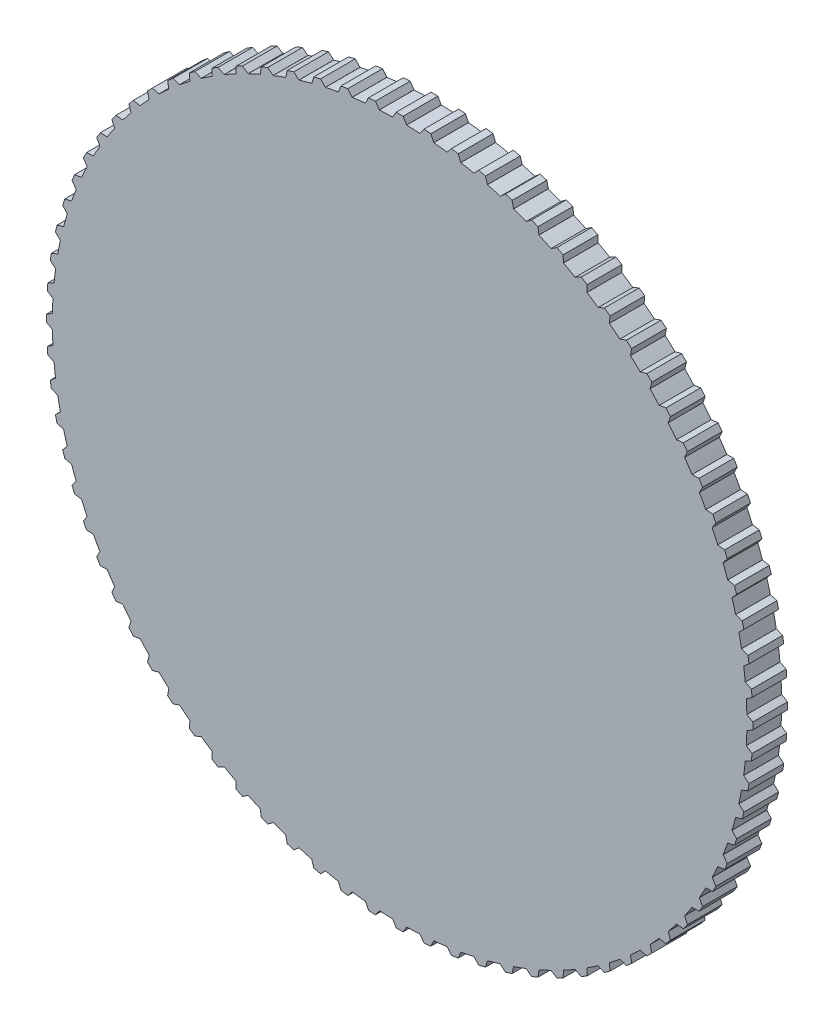
SolidWorks part; units mm, degrees
ref_plane "Front Plane" through (0, 0, 0) normal (0, 0, 1) x (1, 0, 0)
ref_plane "Top Plane" through (0, 0, 0) normal (0, 1, 0) x (1, 0, 0)
ref_plane "Right Plane" through (0, 0, 0) normal (1, 0, 0) x (0, 0, -1)
sketch "Sketch1" plane through (0, 0, 0) normal (0, 0, 1) x (1, 0, 0)
  line L1 (0, 101.7) -> (1, 101.7)
  line L2 (0, 101.7) -> (-1, 101.7)
  line L5 (-1, 101.7) -> (-2, 100)
  line L6 (1, 101.7) -> (2, 100)
  line L7 (-2, 100) -> (-1.9996, 99.98)
  line L8 (2, 100) -> (1.9996, 99.98)
  line L9 (6.9824, 101.465) -> (5.8521, 99.8487)
  line L10 (7.9793, 101.3865) -> (6.9824, 101.465)
  line L11 (7.9793, 101.3865) -> (8.9762, 101.308)
  line L12 (8.9762, 101.308) -> (9.8397, 99.5348)
  line L13 (5.8521, 99.8487) -> (5.8509, 99.8287)
  line L14 (9.8397, 99.5348) -> (9.8378, 99.5149)
  line L15 (14.9217, 100.6043) -> (13.6681, 99.0817)
  line L16 (15.9094, 100.4479) -> (14.9217, 100.6043)
  line L17 (15.9094, 100.4479) -> (16.8971, 100.2915)
  line L18 (16.8971, 100.2915) -> (17.6188, 98.456)
  line L19 (13.6681, 99.0817) -> (13.6653, 99.0619)
  line L20 (17.6188, 98.456) -> (17.6153, 98.4363)
  line L21 (22.769, 99.1235) -> (21.3998, 97.7039)
  line L22 (23.7414, 98.89) -> (22.769, 99.1235)
  line L23 (23.7414, 98.89) -> (24.7138, 98.6566)
  line L24 (24.7138, 98.6566) -> (25.2893, 96.7701)
  line L25 (21.3998, 97.7039) -> (21.3955, 97.6843)
  line L26 (25.2893, 96.7701) -> (25.2842, 96.7508)
  line L27 (30.476, 97.0315) -> (28.9996, 95.7237)
  line L28 (31.427, 96.7224) -> (30.476, 97.0315)
  line L29 (31.427, 96.7224) -> (32.3781, 96.4134)
  line L30 (32.3781, 96.4134) -> (32.8038, 94.4876)
  line L31 (28.9996, 95.7237) -> (28.9938, 95.7045)
  line L32 (32.8038, 94.4876) -> (32.7973, 94.4687)
  line L33 (37.995, 94.3412) -> (36.4206, 93.1533)
  line L34 (38.9189, 93.9585) -> (37.995, 94.3412)
  line L35 (38.9189, 93.9585) -> (39.8428, 93.5759)
  line L36 (39.8428, 93.5759) -> (40.1161, 91.6226)
  line L37 (36.4206, 93.1533) -> (36.4133, 93.1347)
  line L38 (40.1161, 91.6226) -> (40.1081, 91.6043)
  line L39 (45.2798, 91.0694) -> (43.617, 90.0086)
  line L40 (46.1708, 90.6154) -> (45.2798, 91.0694)
  line L41 (46.1708, 90.6154) -> (47.0618, 90.1614)
  line L42 (47.0618, 90.1614) -> (47.1811, 88.1927)
  line L43 (43.617, 90.0086) -> (43.6083, 89.9906)
  line L44 (47.1811, 88.1927) -> (47.1716, 88.175)
  line L45 (52.2855, 87.236) -> (50.5446, 86.309)
  line L46 (53.1381, 86.7135) -> (52.2855, 87.236)
  line L47 (53.1381, 86.7135) -> (53.9907, 86.191)
  line L48 (53.9907, 86.191) -> (53.9551, 84.219)
  line L49 (50.5446, 86.309) -> (50.5345, 86.2918)
  line L50 (53.9551, 84.219) -> (53.9443, 84.2022)
  line L51 (58.9687, 82.8648) -> (57.1605, 82.0773)
  line L52 (59.7778, 82.277) -> (58.9687, 82.8648)
  line L53 (59.7778, 82.277) -> (60.5868, 81.6892)
  line L54 (60.5868, 81.6892) -> (60.3966, 79.7261)
  line L55 (57.1605, 82.0773) -> (57.1491, 82.0609)
  line L56 (60.3966, 79.7261) -> (60.3845, 79.7102)
  line L57 (65.2885, 77.9827) -> (63.424, 77.3395)
  line L58 (66.0489, 77.3333) -> (65.2885, 77.9827)
  line L59 (66.0489, 77.3333) -> (66.8093, 76.6838)
  line L60 (66.8093, 76.6838) -> (66.4656, 74.7417)
  line L61 (63.424, 77.3395) -> (63.4113, 77.324)
  line L62 (66.4656, 74.7417) -> (66.4523, 74.7268)
  line L63 (71.2057, 72.6199) -> (69.2965, 72.1249)
  line L64 (71.9128, 71.9128) -> (71.2057, 72.6199)
  line L65 (71.9128, 71.9128) -> (72.6199, 71.2057)
  line L66 (72.6199, 71.2057) -> (72.1249, 69.2965)
  line L67 (69.2965, 72.1249) -> (69.2826, 72.1105)
  line L68 (72.1249, 69.2965) -> (72.1105, 69.2826)
  line L69 (76.6838, 66.8093) -> (74.7417, 66.4656)
  line L70 (77.3333, 66.0489) -> (76.6838, 66.8093)
  line L71 (77.3333, 66.0489) -> (77.9827, 65.2885)
  line L72 (77.9827, 65.2885) -> (77.3395, 63.424)
  line L73 (74.7417, 66.4656) -> (74.7268, 66.4523)
  line L74 (77.3395, 63.424) -> (77.324, 63.4113)
  line L75 (81.6892, 60.5868) -> (79.7261, 60.3966)
  line L76 (82.277, 59.7778) -> (81.6892, 60.5868)
  line L77 (82.277, 59.7778) -> (82.8648, 58.9687)
  line L78 (82.8648, 58.9687) -> (82.0773, 57.1605)
  line L79 (79.7261, 60.3966) -> (79.7102, 60.3845)
  line L80 (82.0773, 57.1605) -> (82.0609, 57.1491)
  line L81 (86.191, 53.9907) -> (84.219, 53.9551)
  line L82 (86.7135, 53.1381) -> (86.191, 53.9907)
  line L83 (86.7135, 53.1381) -> (87.236, 52.2855)
  line L84 (87.236, 52.2855) -> (86.309, 50.5446)
  line L85 (84.219, 53.9551) -> (84.2022, 53.9443)
  line L86 (86.309, 50.5446) -> (86.2918, 50.5345)
  line L87 (90.1614, 47.0618) -> (88.1927, 47.1811)
  line L88 (90.6154, 46.1708) -> (90.1614, 47.0618)
  line L89 (90.6154, 46.1708) -> (91.0694, 45.2798)
  line L90 (91.0694, 45.2798) -> (90.0086, 43.617)
  line L91 (88.1927, 47.1811) -> (88.175, 47.1716)
  line L92 (90.0086, 43.617) -> (89.9906, 43.6083)
  line L93 (93.5759, 39.8428) -> (91.6226, 40.1161)
  line L94 (93.9585, 38.9189) -> (93.5759, 39.8428)
  line L95 (93.9585, 38.9189) -> (94.3412, 37.995)
  line L96 (94.3412, 37.995) -> (93.1533, 36.4206)
  line L97 (91.6226, 40.1161) -> (91.6043, 40.1081)
  line L98 (93.1533, 36.4206) -> (93.1347, 36.4133)
  line L99 (96.4134, 32.3781) -> (94.4876, 32.8038)
  line L100 (96.7224, 31.427) -> (96.4134, 32.3781)
  line L101 (96.7224, 31.427) -> (97.0315, 30.476)
  line L102 (97.0315, 30.476) -> (95.7237, 28.9996)
  line L103 (94.4876, 32.8038) -> (94.4687, 32.7973)
  line L104 (95.7237, 28.9996) -> (95.7045, 28.9938)
  line L105 (98.6566, 24.7138) -> (96.7701, 25.2893)
  line L106 (98.89, 23.7414) -> (98.6566, 24.7138)
  line L107 (98.89, 23.7414) -> (99.1235, 22.769)
  line L108 (99.1235, 22.769) -> (97.7039, 21.3998)
  line L109 (96.7701, 25.2893) -> (96.7508, 25.2842)
  line L110 (97.7039, 21.3998) -> (97.6843, 21.3955)
  line L111 (100.2915, 16.8971) -> (98.456, 17.6188)
  line L112 (100.4479, 15.9094) -> (100.2915, 16.8971)
  line L113 (100.4479, 15.9094) -> (100.6043, 14.9217)
  line L114 (100.6043, 14.9217) -> (99.0817, 13.6681)
  line L115 (98.456, 17.6188) -> (98.4363, 17.6153)
  line L116 (99.0817, 13.6681) -> (99.0619, 13.6653)
  line L117 (101.308, 8.9762) -> (99.5348, 9.8397)
  line L118 (101.3865, 7.9793) -> (101.308, 8.9762)
  line L119 (101.3865, 7.9793) -> (101.465, 6.9824)
  line L120 (101.465, 6.9824) -> (99.8487, 5.8521)
  line L121 (99.5348, 9.8397) -> (99.5149, 9.8378)
  line L122 (99.8487, 5.8521) -> (99.8287, 5.8509)
  line L123 (101.7, 1) -> (100, 2)
  line L124 (101.7, 0) -> (101.7, 1)
  line L125 (101.7, 0) -> (101.7, -1)
  line L126 (101.7, -1) -> (100, -2)
  line L127 (100, 2) -> (99.98, 1.9996)
  line L128 (100, -2) -> (99.98, -1.9996)
  line L129 (101.465, -6.9824) -> (99.8487, -5.8521)
  line L130 (101.3865, -7.9793) -> (101.465, -6.9824)
  line L131 (101.3865, -7.9793) -> (101.308, -8.9762)
  line L132 (101.308, -8.9762) -> (99.5348, -9.8397)
  line L133 (99.8487, -5.8521) -> (99.8287, -5.8509)
  line L134 (99.5348, -9.8397) -> (99.5149, -9.8378)
  line L135 (100.6043, -14.9217) -> (99.0817, -13.6681)
  line L136 (100.4479, -15.9094) -> (100.6043, -14.9217)
  line L137 (100.4479, -15.9094) -> (100.2915, -16.8971)
  line L138 (100.2915, -16.8971) -> (98.456, -17.6188)
  line L139 (99.0817, -13.6681) -> (99.0619, -13.6653)
  line L140 (98.456, -17.6188) -> (98.4363, -17.6153)
  line L141 (99.1235, -22.769) -> (97.7039, -21.3998)
  line L142 (98.89, -23.7414) -> (99.1235, -22.769)
  line L143 (98.89, -23.7414) -> (98.6566, -24.7138)
  line L144 (98.6566, -24.7138) -> (96.7701, -25.2893)
  line L145 (97.7039, -21.3998) -> (97.6843, -21.3955)
  line L146 (96.7701, -25.2893) -> (96.7508, -25.2842)
  line L147 (97.0315, -30.476) -> (95.7237, -28.9996)
  line L148 (96.7224, -31.427) -> (97.0315, -30.476)
  line L149 (96.7224, -31.427) -> (96.4134, -32.3781)
  line L150 (96.4134, -32.3781) -> (94.4876, -32.8038)
  line L151 (95.7237, -28.9996) -> (95.7045, -28.9938)
  line L152 (94.4876, -32.8038) -> (94.4687, -32.7973)
  line L153 (94.3412, -37.995) -> (93.1533, -36.4206)
  line L154 (93.9585, -38.9189) -> (94.3412, -37.995)
  line L155 (93.9585, -38.9189) -> (93.5759, -39.8428)
  line L156 (93.5759, -39.8428) -> (91.6226, -40.1161)
  line L157 (93.1533, -36.4206) -> (93.1347, -36.4133)
  line L158 (91.6226, -40.1161) -> (91.6043, -40.1081)
  line L159 (91.0694, -45.2798) -> (90.0086, -43.617)
  line L160 (90.6154, -46.1708) -> (91.0694, -45.2798)
  line L161 (90.6154, -46.1708) -> (90.1614, -47.0618)
  line L162 (90.1614, -47.0618) -> (88.1927, -47.1811)
  line L163 (90.0086, -43.617) -> (89.9906, -43.6083)
  line L164 (88.1927, -47.1811) -> (88.175, -47.1716)
  line L165 (87.236, -52.2855) -> (86.309, -50.5446)
  line L166 (86.7135, -53.1381) -> (87.236, -52.2855)
  line L167 (86.7135, -53.1381) -> (86.191, -53.9907)
  line L168 (86.191, -53.9907) -> (84.219, -53.9551)
  line L169 (86.309, -50.5446) -> (86.2918, -50.5345)
  line L170 (84.219, -53.9551) -> (84.2022, -53.9443)
  line L171 (82.8648, -58.9687) -> (82.0773, -57.1605)
  line L172 (82.277, -59.7778) -> (82.8648, -58.9687)
  line L173 (82.277, -59.7778) -> (81.6892, -60.5868)
  line L174 (81.6892, -60.5868) -> (79.7261, -60.3966)
  line L175 (82.0773, -57.1605) -> (82.0609, -57.1491)
  line L176 (79.7261, -60.3966) -> (79.7102, -60.3845)
  line L177 (77.9827, -65.2885) -> (77.3395, -63.424)
  line L178 (77.3333, -66.0489) -> (77.9827, -65.2885)
  line L179 (77.3333, -66.0489) -> (76.6838, -66.8093)
  line L180 (76.6838, -66.8093) -> (74.7417, -66.4656)
  line L181 (77.3395, -63.424) -> (77.324, -63.4113)
  line L182 (74.7417, -66.4656) -> (74.7268, -66.4523)
  line L183 (72.6199, -71.2057) -> (72.1249, -69.2965)
  line L184 (71.9128, -71.9128) -> (72.6199, -71.2057)
  line L185 (71.9128, -71.9128) -> (71.2057, -72.6199)
  line L186 (71.2057, -72.6199) -> (69.2965, -72.1249)
  line L187 (72.1249, -69.2965) -> (72.1105, -69.2826)
  line L188 (69.2965, -72.1249) -> (69.2826, -72.1105)
  line L189 (66.8093, -76.6838) -> (66.4656, -74.7417)
  line L190 (66.0489, -77.3333) -> (66.8093, -76.6838)
  line L191 (66.0489, -77.3333) -> (65.2885, -77.9827)
  line L192 (65.2885, -77.9827) -> (63.424, -77.3395)
  line L193 (66.4656, -74.7417) -> (66.4523, -74.7268)
  line L194 (63.424, -77.3395) -> (63.4113, -77.324)
  line L195 (60.5868, -81.6892) -> (60.3966, -79.7261)
  line L196 (59.7778, -82.277) -> (60.5868, -81.6892)
  line L197 (59.7778, -82.277) -> (58.9687, -82.8648)
  line L198 (58.9687, -82.8648) -> (57.1605, -82.0773)
  line L199 (60.3966, -79.7261) -> (60.3845, -79.7102)
  line L200 (57.1605, -82.0773) -> (57.1491, -82.0609)
  line L201 (53.9907, -86.191) -> (53.9551, -84.219)
  line L202 (53.1381, -86.7135) -> (53.9907, -86.191)
  line L203 (53.1381, -86.7135) -> (52.2855, -87.236)
  line L204 (52.2855, -87.236) -> (50.5446, -86.309)
  line L205 (53.9551, -84.219) -> (53.9443, -84.2022)
  line L206 (50.5446, -86.309) -> (50.5345, -86.2918)
  line L207 (47.0618, -90.1614) -> (47.1811, -88.1927)
  line L208 (46.1708, -90.6154) -> (47.0618, -90.1614)
  line L209 (46.1708, -90.6154) -> (45.2798, -91.0694)
  line L210 (45.2798, -91.0694) -> (43.617, -90.0086)
  line L211 (47.1811, -88.1927) -> (47.1716, -88.175)
  line L212 (43.617, -90.0086) -> (43.6083, -89.9906)
  line L213 (39.8428, -93.5759) -> (40.1161, -91.6226)
  line L214 (38.9189, -93.9585) -> (39.8428, -93.5759)
  line L215 (38.9189, -93.9585) -> (37.995, -94.3412)
  line L216 (37.995, -94.3412) -> (36.4206, -93.1533)
  line L217 (40.1161, -91.6226) -> (40.1081, -91.6043)
  line L218 (36.4206, -93.1533) -> (36.4133, -93.1347)
  line L219 (32.3781, -96.4134) -> (32.8038, -94.4876)
  line L220 (31.427, -96.7224) -> (32.3781, -96.4134)
  line L221 (31.427, -96.7224) -> (30.476, -97.0315)
  line L222 (30.476, -97.0315) -> (28.9996, -95.7237)
  line L223 (32.8038, -94.4876) -> (32.7973, -94.4687)
  line L224 (28.9996, -95.7237) -> (28.9938, -95.7045)
  line L225 (24.7138, -98.6566) -> (25.2893, -96.7701)
  line L226 (23.7414, -98.89) -> (24.7138, -98.6566)
  line L227 (23.7414, -98.89) -> (22.769, -99.1235)
  line L228 (22.769, -99.1235) -> (21.3998, -97.7039)
  line L229 (25.2893, -96.7701) -> (25.2842, -96.7508)
  line L230 (21.3998, -97.7039) -> (21.3955, -97.6843)
  line L231 (16.8971, -100.2915) -> (17.6188, -98.456)
  line L232 (15.9094, -100.4479) -> (16.8971, -100.2915)
  line L233 (15.9094, -100.4479) -> (14.9217, -100.6043)
  line L234 (14.9217, -100.6043) -> (13.6681, -99.0817)
  line L235 (17.6188, -98.456) -> (17.6153, -98.4363)
  line L236 (13.6681, -99.0817) -> (13.6653, -99.0619)
  line L237 (8.9762, -101.308) -> (9.8397, -99.5348)
  line L238 (7.9793, -101.3865) -> (8.9762, -101.308)
  line L239 (7.9793, -101.3865) -> (6.9824, -101.465)
  line L240 (6.9824, -101.465) -> (5.8521, -99.8487)
  line L241 (9.8397, -99.5348) -> (9.8378, -99.5149)
  line L242 (5.8521, -99.8487) -> (5.8509, -99.8287)
  line L243 (1, -101.7) -> (2, -100)
  line L244 (0, -101.7) -> (1, -101.7)
  line L245 (0, -101.7) -> (-1, -101.7)
  line L246 (-1, -101.7) -> (-2, -100)
  line L247 (2, -100) -> (1.9996, -99.98)
  line L248 (-2, -100) -> (-1.9996, -99.98)
  line L249 (-6.9824, -101.465) -> (-5.8521, -99.8487)
  line L250 (-7.9793, -101.3865) -> (-6.9824, -101.465)
  line L251 (-7.9793, -101.3865) -> (-8.9762, -101.308)
  line L252 (-8.9762, -101.308) -> (-9.8397, -99.5348)
  line L253 (-5.8521, -99.8487) -> (-5.8509, -99.8287)
  line L254 (-9.8397, -99.5348) -> (-9.8378, -99.5149)
  line L255 (-14.9217, -100.6043) -> (-13.6681, -99.0817)
  line L256 (-15.9094, -100.4479) -> (-14.9217, -100.6043)
  line L257 (-15.9094, -100.4479) -> (-16.8971, -100.2915)
  line L258 (-16.8971, -100.2915) -> (-17.6188, -98.456)
  line L259 (-13.6681, -99.0817) -> (-13.6653, -99.0619)
  line L260 (-17.6188, -98.456) -> (-17.6153, -98.4363)
  line L261 (-22.769, -99.1235) -> (-21.3998, -97.7039)
  line L262 (-23.7414, -98.89) -> (-22.769, -99.1235)
  line L263 (-23.7414, -98.89) -> (-24.7138, -98.6566)
  line L264 (-24.7138, -98.6566) -> (-25.2893, -96.7701)
  line L265 (-21.3998, -97.7039) -> (-21.3955, -97.6843)
  line L266 (-25.2893, -96.7701) -> (-25.2842, -96.7508)
  line L267 (-30.476, -97.0315) -> (-28.9996, -95.7237)
  line L268 (-31.427, -96.7224) -> (-30.476, -97.0315)
  line L269 (-31.427, -96.7224) -> (-32.3781, -96.4134)
  line L270 (-32.3781, -96.4134) -> (-32.8038, -94.4876)
  line L271 (-28.9996, -95.7237) -> (-28.9938, -95.7045)
  line L272 (-32.8038, -94.4876) -> (-32.7973, -94.4687)
  line L273 (-37.995, -94.3412) -> (-36.4206, -93.1533)
  line L274 (-38.9189, -93.9585) -> (-37.995, -94.3412)
  line L275 (-38.9189, -93.9585) -> (-39.8428, -93.5759)
  line L276 (-39.8428, -93.5759) -> (-40.1161, -91.6226)
  line L277 (-36.4206, -93.1533) -> (-36.4133, -93.1347)
  line L278 (-40.1161, -91.6226) -> (-40.1081, -91.6043)
  line L279 (-45.2798, -91.0694) -> (-43.617, -90.0086)
  line L280 (-46.1708, -90.6154) -> (-45.2798, -91.0694)
  line L281 (-46.1708, -90.6154) -> (-47.0618, -90.1614)
  line L282 (-47.0618, -90.1614) -> (-47.1811, -88.1927)
  line L283 (-43.617, -90.0086) -> (-43.6083, -89.9906)
  line L284 (-47.1811, -88.1927) -> (-47.1716, -88.175)
  line L285 (-52.2855, -87.236) -> (-50.5446, -86.309)
  line L286 (-53.1381, -86.7135) -> (-52.2855, -87.236)
  line L287 (-53.1381, -86.7135) -> (-53.9907, -86.191)
  line L288 (-53.9907, -86.191) -> (-53.9551, -84.219)
  line L289 (-50.5446, -86.309) -> (-50.5345, -86.2918)
  line L290 (-53.9551, -84.219) -> (-53.9443, -84.2022)
  line L291 (-58.9687, -82.8648) -> (-57.1605, -82.0773)
  line L292 (-59.7778, -82.277) -> (-58.9687, -82.8648)
  line L293 (-59.7778, -82.277) -> (-60.5868, -81.6892)
  line L294 (-60.5868, -81.6892) -> (-60.3966, -79.7261)
  line L295 (-57.1605, -82.0773) -> (-57.1491, -82.0609)
  line L296 (-60.3966, -79.7261) -> (-60.3845, -79.7102)
  line L297 (-65.2885, -77.9827) -> (-63.424, -77.3395)
  line L298 (-66.0489, -77.3333) -> (-65.2885, -77.9827)
  line L299 (-66.0489, -77.3333) -> (-66.8093, -76.6838)
  line L300 (-66.8093, -76.6838) -> (-66.4656, -74.7417)
  line L301 (-63.424, -77.3395) -> (-63.4113, -77.324)
  line L302 (-66.4656, -74.7417) -> (-66.4523, -74.7268)
  line L303 (-71.2057, -72.6199) -> (-69.2965, -72.1249)
  line L304 (-71.9128, -71.9128) -> (-71.2057, -72.6199)
  line L305 (-71.9128, -71.9128) -> (-72.6199, -71.2057)
  line L306 (-72.6199, -71.2057) -> (-72.1249, -69.2965)
  line L307 (-69.2965, -72.1249) -> (-69.2826, -72.1105)
  line L308 (-72.1249, -69.2965) -> (-72.1105, -69.2826)
  line L309 (-76.6838, -66.8093) -> (-74.7417, -66.4656)
  line L310 (-77.3333, -66.0489) -> (-76.6838, -66.8093)
  line L311 (-77.3333, -66.0489) -> (-77.9827, -65.2885)
  line L312 (-77.9827, -65.2885) -> (-77.3395, -63.424)
  line L313 (-74.7417, -66.4656) -> (-74.7268, -66.4523)
  line L314 (-77.3395, -63.424) -> (-77.324, -63.4113)
  line L315 (-81.6892, -60.5868) -> (-79.7261, -60.3966)
  line L316 (-82.277, -59.7778) -> (-81.6892, -60.5868)
  line L317 (-82.277, -59.7778) -> (-82.8648, -58.9687)
  line L318 (-82.8648, -58.9687) -> (-82.0773, -57.1605)
  line L319 (-79.7261, -60.3966) -> (-79.7102, -60.3845)
  line L320 (-82.0773, -57.1605) -> (-82.0609, -57.1491)
  line L321 (-86.191, -53.9907) -> (-84.219, -53.9551)
  line L322 (-86.7135, -53.1381) -> (-86.191, -53.9907)
  line L323 (-86.7135, -53.1381) -> (-87.236, -52.2855)
  line L324 (-87.236, -52.2855) -> (-86.309, -50.5446)
  line L325 (-84.219, -53.9551) -> (-84.2022, -53.9443)
  line L326 (-86.309, -50.5446) -> (-86.2918, -50.5345)
  line L327 (-90.1614, -47.0618) -> (-88.1927, -47.1811)
  line L328 (-90.6154, -46.1708) -> (-90.1614, -47.0618)
  line L329 (-90.6154, -46.1708) -> (-91.0694, -45.2798)
  line L330 (-91.0694, -45.2798) -> (-90.0086, -43.617)
  line L331 (-88.1927, -47.1811) -> (-88.175, -47.1716)
  line L332 (-90.0086, -43.617) -> (-89.9906, -43.6083)
  line L333 (-93.5759, -39.8428) -> (-91.6226, -40.1161)
  line L334 (-93.9585, -38.9189) -> (-93.5759, -39.8428)
  line L335 (-93.9585, -38.9189) -> (-94.3412, -37.995)
  line L336 (-94.3412, -37.995) -> (-93.1533, -36.4206)
  line L337 (-91.6226, -40.1161) -> (-91.6043, -40.1081)
  line L338 (-93.1533, -36.4206) -> (-93.1347, -36.4133)
  line L339 (-96.4134, -32.3781) -> (-94.4876, -32.8038)
  line L340 (-96.7224, -31.427) -> (-96.4134, -32.3781)
  line L341 (-96.7224, -31.427) -> (-97.0315, -30.476)
  line L342 (-97.0315, -30.476) -> (-95.7237, -28.9996)
  line L343 (-94.4876, -32.8038) -> (-94.4687, -32.7973)
  line L344 (-95.7237, -28.9996) -> (-95.7045, -28.9938)
  line L345 (-98.6566, -24.7138) -> (-96.7701, -25.2893)
  line L346 (-98.89, -23.7414) -> (-98.6566, -24.7138)
  line L347 (-98.89, -23.7414) -> (-99.1235, -22.769)
  line L348 (-99.1235, -22.769) -> (-97.7039, -21.3998)
  line L349 (-96.7701, -25.2893) -> (-96.7508, -25.2842)
  line L350 (-97.7039, -21.3998) -> (-97.6843, -21.3955)
  line L351 (-100.2915, -16.8971) -> (-98.456, -17.6188)
  line L352 (-100.4479, -15.9094) -> (-100.2915, -16.8971)
  line L353 (-100.4479, -15.9094) -> (-100.6043, -14.9217)
  line L354 (-100.6043, -14.9217) -> (-99.0817, -13.6681)
  line L355 (-98.456, -17.6188) -> (-98.4363, -17.6153)
  line L356 (-99.0817, -13.6681) -> (-99.0619, -13.6653)
  line L357 (-101.308, -8.9762) -> (-99.5348, -9.8397)
  line L358 (-101.3865, -7.9793) -> (-101.308, -8.9762)
  line L359 (-101.3865, -7.9793) -> (-101.465, -6.9824)
  line L360 (-101.465, -6.9824) -> (-99.8487, -5.8521)
  line L361 (-99.5348, -9.8397) -> (-99.5149, -9.8378)
  line L362 (-99.8487, -5.8521) -> (-99.8287, -5.8509)
  line L363 (-101.7, -1) -> (-100, -2)
  line L364 (-101.7, 0) -> (-101.7, -1)
  line L365 (-101.7, 0) -> (-101.7, 1)
  line L366 (-101.7, 1) -> (-100, 2)
  line L367 (-100, -2) -> (-99.98, -1.9996)
  line L368 (-100, 2) -> (-99.98, 1.9996)
  line L369 (-101.465, 6.9824) -> (-99.8487, 5.8521)
  line L370 (-101.3865, 7.9793) -> (-101.465, 6.9824)
  line L371 (-101.3865, 7.9793) -> (-101.308, 8.9762)
  line L372 (-101.308, 8.9762) -> (-99.5348, 9.8397)
  line L373 (-99.8487, 5.8521) -> (-99.8287, 5.8509)
  line L374 (-99.5348, 9.8397) -> (-99.5149, 9.8378)
  line L375 (-100.6043, 14.9217) -> (-99.0817, 13.6681)
  line L376 (-100.4479, 15.9094) -> (-100.6043, 14.9217)
  line L377 (-100.4479, 15.9094) -> (-100.2915, 16.8971)
  line L378 (-100.2915, 16.8971) -> (-98.456, 17.6188)
  line L379 (-99.0817, 13.6681) -> (-99.0619, 13.6653)
  line L380 (-98.456, 17.6188) -> (-98.4363, 17.6153)
  line L381 (-99.1235, 22.769) -> (-97.7039, 21.3998)
  line L382 (-98.89, 23.7414) -> (-99.1235, 22.769)
  line L383 (-98.89, 23.7414) -> (-98.6566, 24.7138)
  line L384 (-98.6566, 24.7138) -> (-96.7701, 25.2893)
  line L385 (-97.7039, 21.3998) -> (-97.6843, 21.3955)
  line L386 (-96.7701, 25.2893) -> (-96.7508, 25.2842)
  line L387 (-97.0315, 30.476) -> (-95.7237, 28.9996)
  line L388 (-96.7224, 31.427) -> (-97.0315, 30.476)
  line L389 (-96.7224, 31.427) -> (-96.4134, 32.3781)
  line L390 (-96.4134, 32.3781) -> (-94.4876, 32.8038)
  line L391 (-95.7237, 28.9996) -> (-95.7045, 28.9938)
  line L392 (-94.4876, 32.8038) -> (-94.4687, 32.7973)
  line L393 (-94.3412, 37.995) -> (-93.1533, 36.4206)
  line L394 (-93.9585, 38.9189) -> (-94.3412, 37.995)
  line L395 (-93.9585, 38.9189) -> (-93.5759, 39.8428)
  line L396 (-93.5759, 39.8428) -> (-91.6226, 40.1161)
  line L397 (-93.1533, 36.4206) -> (-93.1347, 36.4133)
  line L398 (-91.6226, 40.1161) -> (-91.6043, 40.1081)
  line L399 (-91.0694, 45.2798) -> (-90.0086, 43.617)
  line L400 (-90.6154, 46.1708) -> (-91.0694, 45.2798)
  line L401 (-90.6154, 46.1708) -> (-90.1614, 47.0618)
  line L402 (-90.1614, 47.0618) -> (-88.1927, 47.1811)
  line L403 (-90.0086, 43.617) -> (-89.9906, 43.6083)
  line L404 (-88.1927, 47.1811) -> (-88.175, 47.1716)
  line L405 (-87.236, 52.2855) -> (-86.309, 50.5446)
  line L406 (-86.7135, 53.1381) -> (-87.236, 52.2855)
  line L407 (-86.7135, 53.1381) -> (-86.191, 53.9907)
  line L408 (-86.191, 53.9907) -> (-84.219, 53.9551)
  line L409 (-86.309, 50.5446) -> (-86.2918, 50.5345)
  line L410 (-84.219, 53.9551) -> (-84.2022, 53.9443)
  line L411 (-82.8648, 58.9687) -> (-82.0773, 57.1605)
  line L412 (-82.277, 59.7778) -> (-82.8648, 58.9687)
  line L413 (-82.277, 59.7778) -> (-81.6892, 60.5868)
  line L414 (-81.6892, 60.5868) -> (-79.7261, 60.3966)
  line L415 (-82.0773, 57.1605) -> (-82.0609, 57.1491)
  line L416 (-79.7261, 60.3966) -> (-79.7102, 60.3845)
  line L417 (-77.9827, 65.2885) -> (-77.3395, 63.424)
  line L418 (-77.3333, 66.0489) -> (-77.9827, 65.2885)
  line L419 (-77.3333, 66.0489) -> (-76.6838, 66.8093)
  line L420 (-76.6838, 66.8093) -> (-74.7417, 66.4656)
  line L421 (-77.3395, 63.424) -> (-77.324, 63.4113)
  line L422 (-74.7417, 66.4656) -> (-74.7268, 66.4523)
  line L423 (-72.6199, 71.2057) -> (-72.1249, 69.2965)
  line L424 (-71.9128, 71.9128) -> (-72.6199, 71.2057)
  line L425 (-71.9128, 71.9128) -> (-71.2057, 72.6199)
  line L426 (-71.2057, 72.6199) -> (-69.2965, 72.1249)
  line L427 (-72.1249, 69.2965) -> (-72.1105, 69.2826)
  line L428 (-69.2965, 72.1249) -> (-69.2826, 72.1105)
  line L429 (-66.8093, 76.6838) -> (-66.4656, 74.7417)
  line L430 (-66.0489, 77.3333) -> (-66.8093, 76.6838)
  line L431 (-66.0489, 77.3333) -> (-65.2885, 77.9827)
  line L432 (-65.2885, 77.9827) -> (-63.424, 77.3395)
  line L433 (-66.4656, 74.7417) -> (-66.4523, 74.7268)
  line L434 (-63.424, 77.3395) -> (-63.4113, 77.324)
  line L435 (-60.5868, 81.6892) -> (-60.3966, 79.7261)
  line L436 (-59.7778, 82.277) -> (-60.5868, 81.6892)
  line L437 (-59.7778, 82.277) -> (-58.9687, 82.8648)
  line L438 (-58.9687, 82.8648) -> (-57.1605, 82.0773)
  line L439 (-60.3966, 79.7261) -> (-60.3845, 79.7102)
  line L440 (-57.1605, 82.0773) -> (-57.1491, 82.0609)
  line L441 (-53.9907, 86.191) -> (-53.9551, 84.219)
  line L442 (-53.1381, 86.7135) -> (-53.9907, 86.191)
  line L443 (-53.1381, 86.7135) -> (-52.2855, 87.236)
  line L444 (-52.2855, 87.236) -> (-50.5446, 86.309)
  line L445 (-53.9551, 84.219) -> (-53.9443, 84.2022)
  line L446 (-50.5446, 86.309) -> (-50.5345, 86.2918)
  line L447 (-47.0618, 90.1614) -> (-47.1811, 88.1927)
  line L448 (-46.1708, 90.6154) -> (-47.0618, 90.1614)
  line L449 (-46.1708, 90.6154) -> (-45.2798, 91.0694)
  line L450 (-45.2798, 91.0694) -> (-43.617, 90.0086)
  line L451 (-47.1811, 88.1927) -> (-47.1716, 88.175)
  line L452 (-43.617, 90.0086) -> (-43.6083, 89.9906)
  line L453 (-39.8428, 93.5759) -> (-40.1161, 91.6226)
  line L454 (-38.9189, 93.9585) -> (-39.8428, 93.5759)
  line L455 (-38.9189, 93.9585) -> (-37.995, 94.3412)
  line L456 (-37.995, 94.3412) -> (-36.4206, 93.1533)
  line L457 (-40.1161, 91.6226) -> (-40.1081, 91.6043)
  line L458 (-36.4206, 93.1533) -> (-36.4133, 93.1347)
  line L459 (-32.3781, 96.4134) -> (-32.8038, 94.4876)
  line L460 (-31.427, 96.7224) -> (-32.3781, 96.4134)
  line L461 (-31.427, 96.7224) -> (-30.476, 97.0315)
  line L462 (-30.476, 97.0315) -> (-28.9996, 95.7237)
  line L463 (-32.8038, 94.4876) -> (-32.7973, 94.4687)
  line L464 (-28.9996, 95.7237) -> (-28.9938, 95.7045)
  line L465 (-24.7138, 98.6566) -> (-25.2893, 96.7701)
  line L466 (-23.7414, 98.89) -> (-24.7138, 98.6566)
  line L467 (-23.7414, 98.89) -> (-22.769, 99.1235)
  line L468 (-22.769, 99.1235) -> (-21.3998, 97.7039)
  line L469 (-25.2893, 96.7701) -> (-25.2842, 96.7508)
  line L470 (-21.3998, 97.7039) -> (-21.3955, 97.6843)
  line L471 (-16.8971, 100.2915) -> (-17.6188, 98.456)
  line L472 (-15.9094, 100.4479) -> (-16.8971, 100.2915)
  line L473 (-15.9094, 100.4479) -> (-14.9217, 100.6043)
  line L474 (-14.9217, 100.6043) -> (-13.6681, 99.0817)
  line L475 (-17.6188, 98.456) -> (-17.6153, 98.4363)
  line L476 (-13.6681, 99.0817) -> (-13.6653, 99.0619)
  line L477 (-8.9762, 101.308) -> (-9.8397, 99.5348)
  line L478 (-7.9793, 101.3865) -> (-8.9762, 101.308)
  line L479 (-7.9793, 101.3865) -> (-6.9824, 101.465)
  line L480 (-6.9824, 101.465) -> (-5.8521, 99.8487)
  line L481 (-9.8397, 99.5348) -> (-9.8378, 99.5149)
  line L482 (-5.8521, 99.8487) -> (-5.8509, 99.8287)
  arc A0 (-1.9996, 99.98) -> (-5.8509, 99.8287) centre (0, 0) ccw
  arc A1 (-9.8378, 99.5149) -> (-13.6653, 99.0619) centre (0, 0) ccw
  arc A2 (-17.6153, 98.4363) -> (-21.3955, 97.6843) centre (0, 0) ccw
  arc A3 (-25.2842, 96.7508) -> (-28.9938, 95.7045) centre (0, 0) ccw
  arc A4 (5.8509, 99.8287) -> (1.9996, 99.98) centre (0, 0) ccw
  arc A5 (13.6653, 99.0619) -> (9.8378, 99.5149) centre (0, 0) ccw
  arc A6 (50.5345, 86.2918) -> (47.1716, 88.175) centre (0, 0) ccw
  arc A7 (43.6083, 89.9906) -> (40.1081, 91.6043) centre (0, 0) ccw
  arc A8 (36.4133, 93.1347) -> (32.7973, 94.4687) centre (0, 0) ccw
  arc A9 (28.9938, 95.7045) -> (25.2842, 96.7508) centre (0, 0) ccw
  arc A10 (21.3955, 97.6843) -> (17.6153, 98.4363) centre (0, 0) ccw
  arc A11 (-99.0619, 13.6653) -> (-99.5149, 9.8378) centre (0, 0) ccw
  arc A12 (-97.6843, 21.3955) -> (-98.4363, 17.6153) centre (0, 0) ccw
  arc A13 (-95.7045, 28.9938) -> (-96.7508, 25.2842) centre (0, 0) ccw
  arc A14 (-93.1347, 36.4133) -> (-94.4687, 32.7973) centre (0, 0) ccw
  arc A15 (-89.9906, 43.6083) -> (-91.6043, 40.1081) centre (0, 0) ccw
  arc A16 (-86.2918, 50.5345) -> (-88.175, 47.1716) centre (0, 0) ccw
  arc A17 (-82.0609, 57.1491) -> (-84.2022, 53.9443) centre (0, 0) ccw
  arc A18 (-77.324, 63.4113) -> (-79.7102, 60.3845) centre (0, 0) ccw
  arc A19 (-72.1105, 69.2826) -> (-74.7268, 66.4523) centre (0, 0) ccw
  arc A20 (-66.4523, 74.7268) -> (-69.2826, 72.1105) centre (0, 0) ccw
  arc A21 (-60.3845, 79.7102) -> (-63.4113, 77.324) centre (0, 0) ccw
  arc A22 (-53.9443, 84.2022) -> (-57.1491, 82.0609) centre (0, 0) ccw
  arc A23 (-47.1716, 88.175) -> (-50.5345, 86.2918) centre (0, 0) ccw
  arc A24 (-40.1081, 91.6043) -> (-43.6083, 89.9906) centre (0, 0) ccw
  arc A25 (-32.7973, 94.4687) -> (-36.4133, 93.1347) centre (0, 0) ccw
  arc A26 (91.6043, 40.1081) -> (89.9906, 43.6083) centre (0, 0) ccw
  arc A27 (88.175, 47.1716) -> (86.2918, 50.5345) centre (0, 0) ccw
  arc A28 (84.2022, 53.9443) -> (82.0609, 57.1491) centre (0, 0) ccw
  arc A29 (74.7268, 66.4523) -> (72.1105, 69.2826) centre (0, 0) ccw
  arc A30 (69.2826, 72.1105) -> (66.4523, 74.7268) centre (0, 0) ccw
  arc A31 (63.4113, 77.324) -> (60.3845, 79.7102) centre (0, 0) ccw
  arc A32 (57.1491, 82.0609) -> (53.9443, 84.2022) centre (0, 0) ccw
  arc A33 (79.7102, 60.3845) -> (77.324, 63.4113) centre (0, 0) ccw
  arc A34 (94.4687, 32.7973) -> (93.1347, 36.4133) centre (0, 0) ccw
  arc A35 (93.1347, -36.4133) -> (94.4687, -32.7973) centre (0, 0) ccw
  arc A36 (95.7045, -28.9938) -> (96.7508, -25.2842) centre (0, 0) ccw
  arc A37 (97.6843, -21.3955) -> (98.4363, -17.6153) centre (0, 0) ccw
  arc A38 (99.0619, -13.6653) -> (99.5149, -9.8378) centre (0, 0) ccw
  arc A39 (96.7508, 25.2842) -> (95.7045, 28.9938) centre (0, 0) ccw
  arc A40 (98.4363, 17.6153) -> (97.6843, 21.3955) centre (0, 0) ccw
  arc A41 (99.5149, 9.8378) -> (99.0619, 13.6653) centre (0, 0) ccw
  arc A42 (99.98, 1.9996) -> (99.8287, 5.8509) centre (0, 0) ccw
  arc A43 (99.8287, -5.8509) -> (99.98, -1.9996) centre (0, 0) ccw
  arc A44 (-99.8287, 5.8509) -> (-99.98, 1.9996) centre (0, 0) ccw
  arc A45 (-99.98, -1.9996) -> (-99.8287, -5.8509) centre (0, 0) ccw
  arc A46 (-99.5149, -9.8378) -> (-99.0619, -13.6653) centre (0, 0) ccw
  arc A47 (-98.4363, -17.6153) -> (-97.6843, -21.3955) centre (0, 0) ccw
  arc A48 (-96.7508, -25.2842) -> (-95.7045, -28.9938) centre (0, 0) ccw
  arc A49 (-94.4687, -32.7973) -> (-93.1347, -36.4133) centre (0, 0) ccw
  arc A50 (-91.6043, -40.1081) -> (-89.9906, -43.6083) centre (0, 0) ccw
  arc A51 (-88.175, -47.1716) -> (-86.2918, -50.5345) centre (0, 0) ccw
  arc A52 (-84.2022, -53.9443) -> (-82.0609, -57.1491) centre (0, 0) ccw
  arc A53 (-79.7102, -60.3845) -> (-77.324, -63.4113) centre (0, 0) ccw
  arc A54 (-74.7268, -66.4523) -> (-72.1105, -69.2826) centre (0, 0) ccw
  arc A55 (-69.2826, -72.1105) -> (-66.4523, -74.7268) centre (0, 0) ccw
  arc A56 (-63.4113, -77.324) -> (-60.3845, -79.7102) centre (0, 0) ccw
  arc A57 (-57.1491, -82.0609) -> (-53.9443, -84.2022) centre (0, 0) ccw
  arc A58 (-50.5345, -86.2918) -> (-47.1716, -88.175) centre (0, 0) ccw
  arc A59 (-43.6083, -89.9906) -> (-40.1081, -91.6043) centre (0, 0) ccw
  arc A60 (-36.4133, -93.1347) -> (-32.7973, -94.4687) centre (0, 0) ccw
  arc A61 (-28.9938, -95.7045) -> (-25.2842, -96.7508) centre (0, 0) ccw
  arc A62 (-21.3955, -97.6843) -> (-17.6153, -98.4363) centre (0, 0) ccw
  arc A63 (-13.6653, -99.0619) -> (-9.8378, -99.5149) centre (0, 0) ccw
  arc A64 (-5.8509, -99.8287) -> (-1.9996, -99.98) centre (0, 0) ccw
  arc A65 (1.9996, -99.98) -> (5.8509, -99.8287) centre (0, 0) ccw
  arc A66 (9.8378, -99.5149) -> (13.6653, -99.0619) centre (0, 0) ccw
  arc A67 (17.6153, -98.4363) -> (21.3955, -97.6843) centre (0, 0) ccw
  arc A68 (25.2842, -96.7508) -> (28.9938, -95.7045) centre (0, 0) ccw
  arc A69 (89.9906, -43.6083) -> (91.6043, -40.1081) centre (0, 0) ccw
  arc A70 (86.2918, -50.5345) -> (88.175, -47.1716) centre (0, 0) ccw
  arc A71 (82.0609, -57.1491) -> (84.2022, -53.9443) centre (0, 0) ccw
  arc A72 (77.324, -63.4113) -> (79.7102, -60.3845) centre (0, 0) ccw
  arc A73 (72.1105, -69.2826) -> (74.7268, -66.4523) centre (0, 0) ccw
  arc A74 (66.4523, -74.7268) -> (69.2826, -72.1105) centre (0, 0) ccw
  arc A75 (60.3845, -79.7102) -> (63.4113, -77.324) centre (0, 0) ccw
  arc A76 (53.9443, -84.2022) -> (57.1491, -82.0609) centre (0, 0) ccw
  arc A77 (47.1716, -88.175) -> (50.5345, -86.2918) centre (0, 0) ccw
  arc A78 (40.1081, -91.6043) -> (43.6083, -89.9906) centre (0, 0) ccw
  arc A79 (32.7973, -94.4687) -> (36.4133, -93.1347) centre (0, 0) ccw
  point P5 (0, 0)
  point P10 (0, 0)
  point P11 (0, 0)
  point P407 (0, 0)
  point P408 (0, 0)
  dimension "D6" = 200
  dimension "D2" = 1
  dimension "D3" = 1
  dimension "D7" = 80
extrude "Boss-Extrude1" add sketch "Sketch1" along normal blind 10
